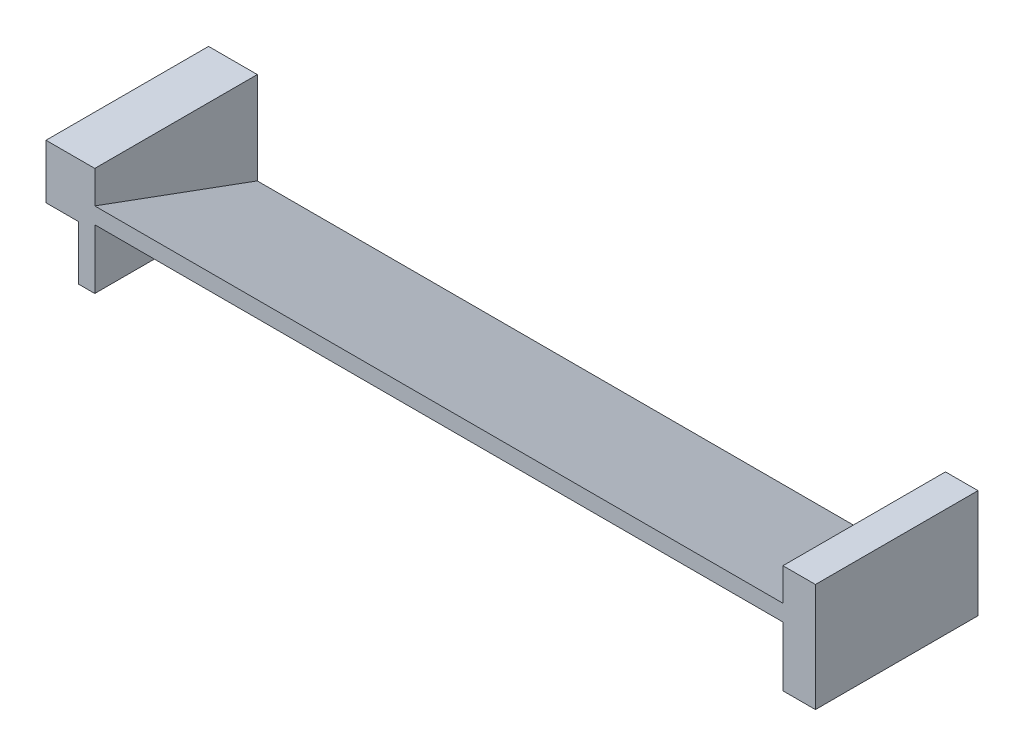
SolidWorks part; units mm, degrees
ref_plane "정면" through (0, 0, 0) normal (0, 0, 1) x (1, 0, 0)
ref_plane "윗면" through (0, 0, 0) normal (0, 1, 0) x (1, 0, 0)
ref_plane "우측면" through (0, 0, 0) normal (1, 0, 0) x (0, 0, -1)
sketch "스케치5" plane through (0, 0, 0) normal (0, 1, 0) x (1, 0, 0)
  line L0 (-132.2141, 0) -> (147.871, 0) construction
  line L1 (0, 68.4002) -> (0, -85.955) construction
  line L2 (71, 15) -> (65, 15)
  line L3 (-71, -15) -> (-65, -15)
  line L4 (-71, -15) -> (-71, 15)
  line L5 (-71, 15) -> (-65, 15)
  line L6 (-65, -15) -> (-65, 15)
  line L7 (-71, -15) -> (-65, 15) construction
  line L8 (-71, 15) -> (-65, -15) construction
  line L9 (65, -15) -> (65, 15)
  line L10 (71, -15) -> (65, -15)
  line L11 (71, -15) -> (71, 15)
  point P5 (-68, 0)
  dimension "D1" = 71
  dimension "D2" = 30
  dimension "D3" = 6
extrude "보스-돌출2" add sketch "스케치5" against normal blind 10
sketch "스케치6" plane through (0, -10, 0) normal (0, -1, 0) x (1, 0, 0)
  line L1 (65, 15) -> (71, 15)
  line L2 (65, 15) -> (65, -15)
  line L3 (65, -15) -> (71, -15)
  line L4 (71, 15) -> (71, -15)
extrude "보스-돌출3" add sketch "스케치6" along normal blind 10
sketch "스케치8" plane through (-65, 0, 0) normal (1, 0, 0) x (0, 0, -1)
  line L0 (15, -14) -> (15, -20)
  line L1 (-15, 0) -> (15, 0)
  line L2 (-15, 0) -> (-15, -20)
  line L3 (-15, -20) -> (15, -20)
  line L4 (15, 0) -> (15, -14)
extrude "보스-돌출4" add sketch "스케치8" along normal blind 3
sketch "스케치7" plane through (65, 0, 0) normal (-1, 0, 0) x (0, 0, 1)
  line L1 (-15, -17) -> (-15, -20)
  line L2 (-15, -17) -> (15, -6)
  line L3 (15, -20) -> (15, 0) construction
  line L4 (15, -6) -> (15, -9)
  line L5 (15, -9) -> (-15, -20)
  line L6 (-15, -20) -> (-15, -10) construction
  line L7 (-15, -10) -> (-15, 0) construction
  line L8 (15, -20) -> (-15, -20) construction
  point P4 (0, 0)
  point P11 (-15, -17.9848)
  point P12 (0, 0)
  dimension "D1" = 11
  dimension "D2" = 3
extrude "보스-돌출5" add sketch "스케치7" along normal up to next
